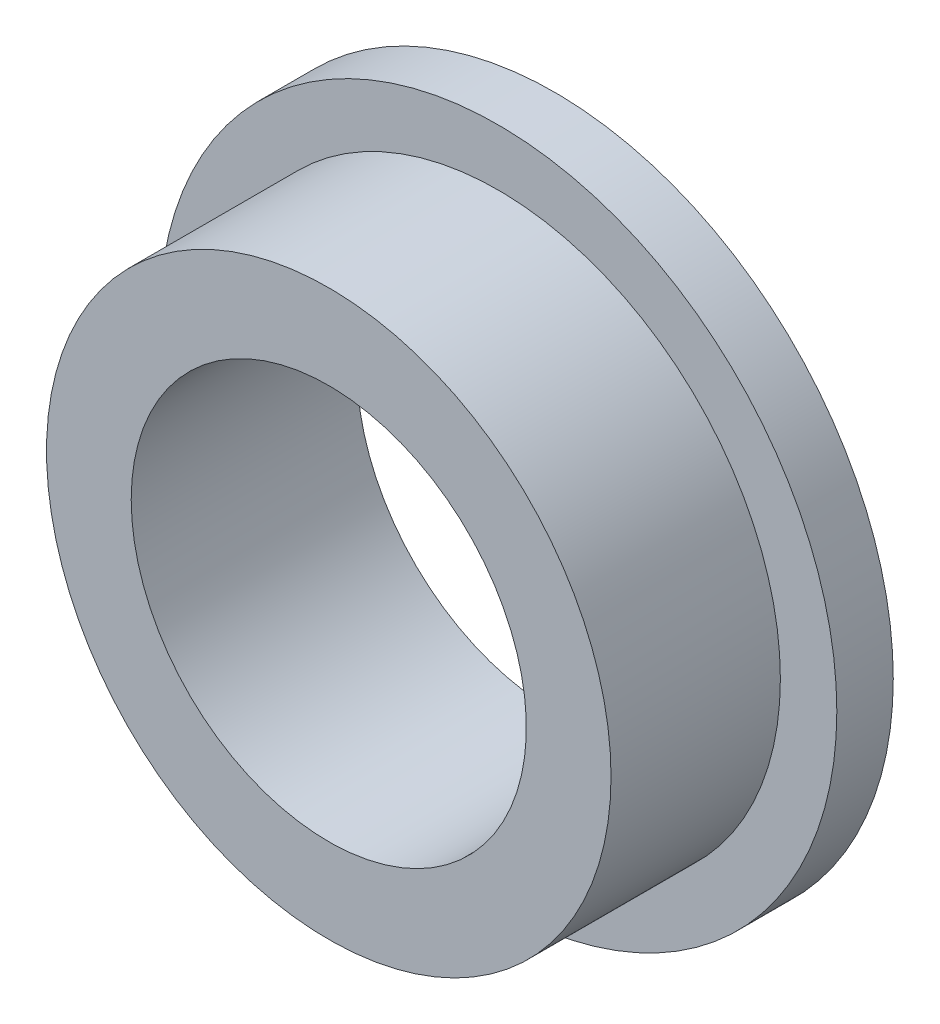
SolidWorks part; units mm, degrees
material "Латунь"
ref_plane "Спереди" through (0, 0, 0) normal (0, 0, 1) x (1, 0, 0)
ref_plane "Сверху" through (0, 0, 0) normal (0, 1, 0) x (1, 0, 0)
ref_plane "Справа" through (0, 0, 0) normal (1, 0, 0) x (0, 0, -1)
sketch "Эскиз2" plane through (0, 0, 0) normal (0, 0, 1) x (1, 0, 0)
  circle A0 centre (0, 0) radius 6
  dimension "D1" = 12
extrude "Бобышка-Вытянуть1" add sketch "Эскиз2" along normal blind 1
sketch "Эскиз3" plane through (0, 0, 1) normal (0, 0, 1) x (1, 0, 0)
  circle A2 centre (0, 0) radius 5
  circle A3 centre (0, 0) radius 5
  dimension "D1" = 1
extrude "Бобышка-Вытянуть2" add sketch "Эскиз3" along normal blind 3
sketch "Эскиз4" plane through (0, 0, 0) normal (0, 0, -1) x (-1, 0, 0)
  circle A0 centre (0, 0) radius 3.5
  dimension "D1" = 7
extrude "Вырез-Вытянуть1" cut sketch "Эскиз4" against normal through all
